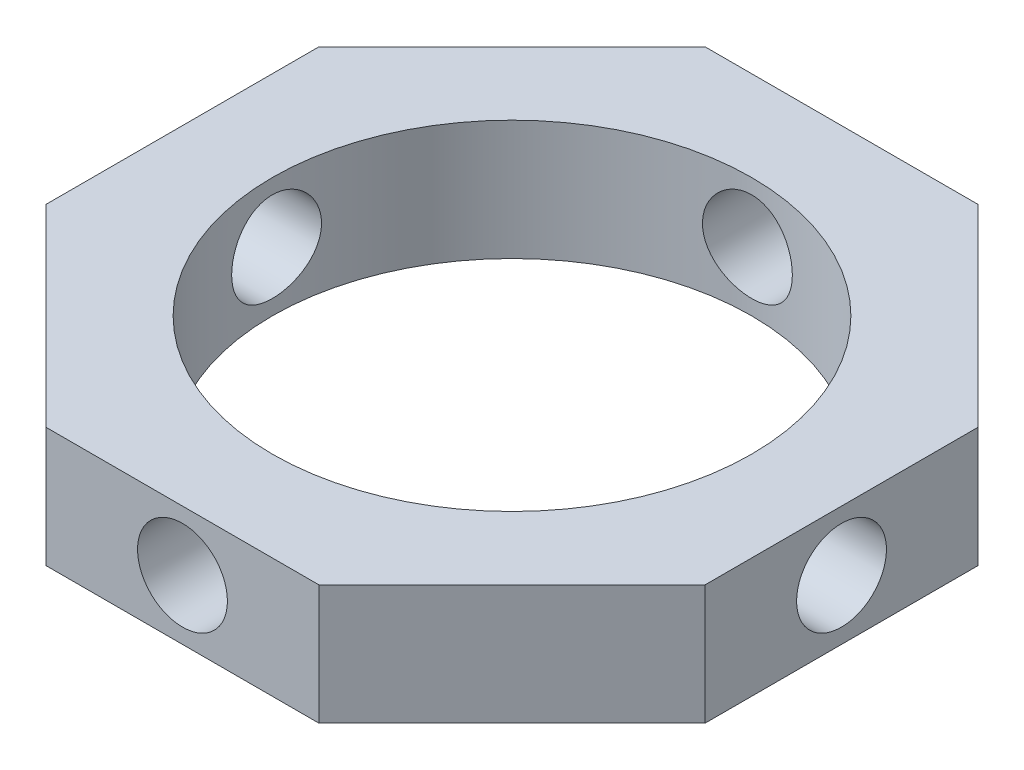
SolidWorks part; units mm, degrees
ref_plane "Front Plane" through (0, 0, 0) normal (0, 0, 1) x (1, 0, 0)
ref_plane "Top Plane" through (0, 0, 0) normal (0, 1, 0) x (1, 0, 0)
ref_plane "Right Plane" through (0, 0, 0) normal (1, 0, 0) x (0, 0, -1)
sketch "Sketch2" plane through (0, 0, 0) normal (0, 1, 0) x (1, 0, 0)
  line L0 (-1000, 0) -> (49000, 0) construction
  line L1 (0, -1000) -> (0, 49000) construction
  line L2 (-923.8795, -382.6834) -> (45270.0971, 18751.4882) construction
  line L4 (69.85, 28.9328) -> (28.9328, 69.85)
  line L5 (28.9328, 69.85) -> (-28.9328, 69.85)
  line L6 (-28.9328, 69.85) -> (-69.85, 28.9328)
  line L7 (-69.85, 28.9328) -> (-69.85, -28.9328)
  line L8 (-69.85, -28.9328) -> (-28.9328, -69.85)
  line L9 (-28.9328, -69.85) -> (28.9328, -69.85)
  line L10 (28.9328, -69.85) -> (69.85, -28.9328)
  line L11 (69.85, -28.9328) -> (69.85, 28.9328)
  circle A0 centre (0, 0) radius 69.85 construction
  circle A1 centre (0, 0) radius 50.8
  dimension "D3" = 101.6
  dimension "D1" = 22.5
  dimension "D2" = 139.7
extrude "Boss-Extrude1" add sketch "Sketch2" along normal blind 25.4
sketch "Sketch3" plane through (0, 0, 69.85) normal (0, 0, 1) x (1, 0, 0)
  line L0 (-28.9328, 0) -> (28.9328, 0) construction
  circle A0 centre (0, 12.7) radius 9.525
  dimension "D2" = 19.05
  dimension "D1" = 12.7
extrude "Cut-Extrude1" cut sketch "Sketch3" against normal through all
sketch "Sketch4" plane through (-69.85, 0, 0) normal (-1, 0, 0) x (0, 0, 1)
  line L0 (-28.9328, 0) -> (28.9328, 0) construction
  circle A0 centre (0, 12.7) radius 9.525
  dimension "D2" = 19.05
  dimension "D1" = 12.7
extrude "Cut-Extrude2" cut sketch "Sketch4" against normal through all contours A0
